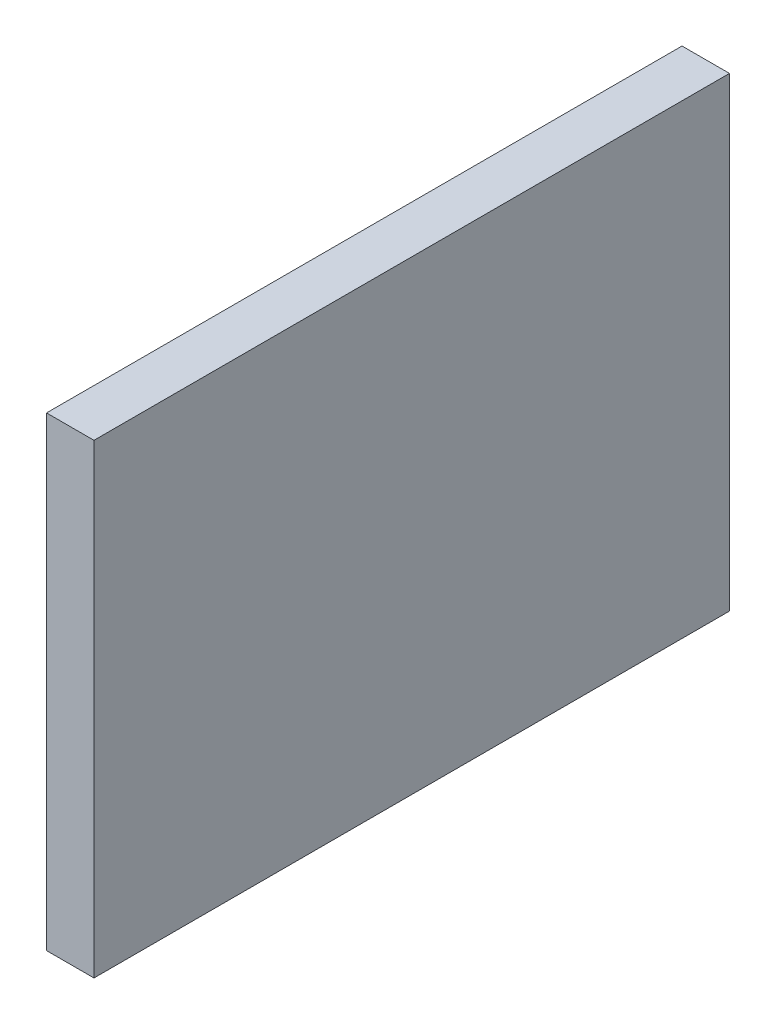
SolidWorks part; units mm, degrees
ref_plane "Front Plane" through (0, 0, 0) normal (0, 0, 1) x (1, 0, 0)
ref_plane "Top Plane" through (0, 0, 0) normal (0, 1, 0) x (1, 0, 0)
ref_plane "Right Plane" through (0, 0, 0) normal (1, 0, 0) x (0, 0, -1)
sketch "Sketch1" plane through (0, 0, 0) normal (1, 0, 0) x (0, 0, -1)
  line L0 (73.66, 53.975) -> (-73.66, -53.975) construction
  line L1 (73.66, 53.975) -> (-73.66, 53.975)
  line L2 (73.66, 53.975) -> (73.66, -53.975)
  line L3 (73.66, -53.975) -> (-73.66, -53.975)
  line L4 (-73.66, 53.975) -> (-73.66, -53.975)
  point P4 (0, 0)
  dimension "D1" = 147.32
  dimension "D2" = 107.95
extrude "Boss-Extrude1" add sketch "Sketch1" against normal blind 11
